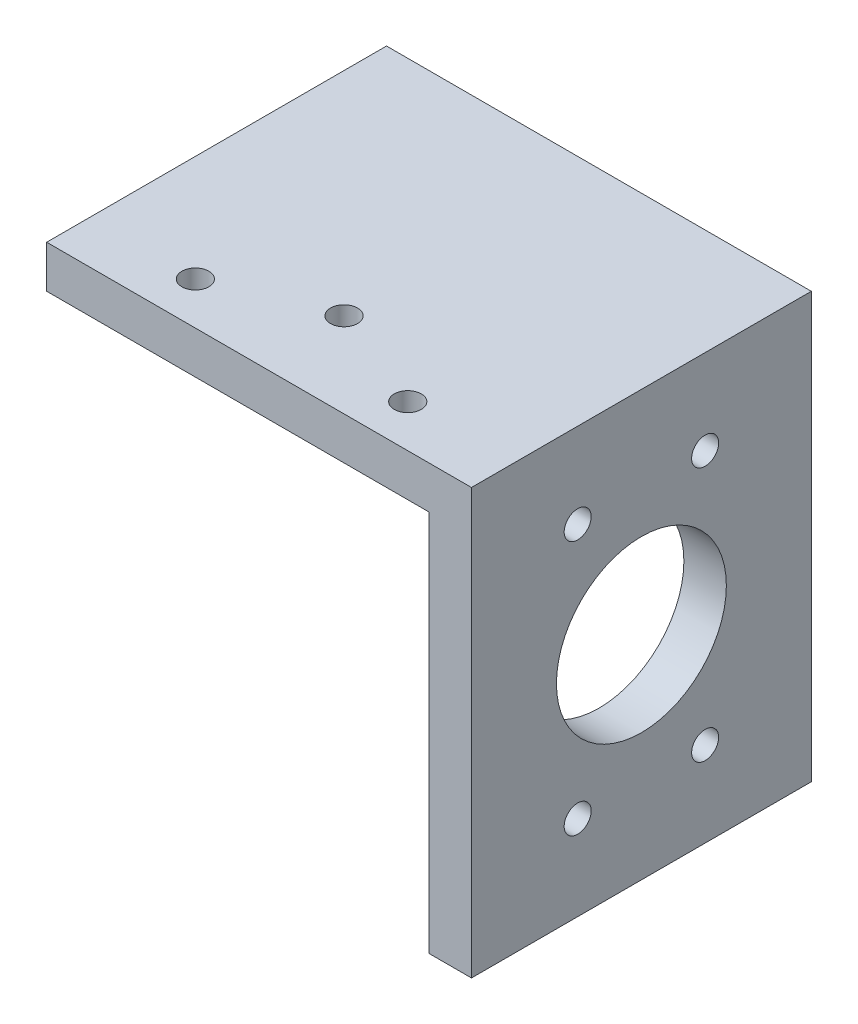
SolidWorks part; units mm, degrees
ref_plane "Front Plane" through (0, 0, 0) normal (0, 0, 1) x (1, 0, 0)
ref_plane "Top Plane" through (0, 0, 0) normal (0, 1, 0) x (1, 0, 0)
ref_plane "Right Plane" through (0, 0, 0) normal (1, 0, 0) x (0, 0, -1)
sketch "Sketch1" plane through (0, 0, 0) normal (0, 0, 1) x (1, 0, 0)
  line L0 (0, 0) -> (63.5, 0)
  line L1 (63.5, 0) -> (63.5, -63.5)
  line L2 (63.5, -63.5) -> (57.15, -63.5)
  line L3 (57.15, -63.5) -> (57.15, -6.35)
  line L4 (57.15, -6.35) -> (0, -6.35)
  line L5 (0, -6.35) -> (0, 0)
  dimension "D1" = 6.35
  dimension "D2" = 6.35
  dimension "D3" = 63.5
  dimension "D4" = 63.5
extrude "Boss-Extrude1" add sketch "Sketch1" along normal blind 50.8
sketch "Sketch2" plane through (63.5, 0, 0) normal (1, 0, 0) x (0, 0, -1)
  line L0 (-50.8, 0) -> (0, 0) construction
  line L5 (-50.8, -63.5) -> (-50.8, 0) construction
  circle A0 centre (-25.4, -31.75) radius 12.7
  dimension "D1" = 25.4
  dimension "D4" = 31.75
  dimension "D5" = 25.4
extrude "Cut-Extrude1" cut sketch "Sketch2" against normal up to next
sketch "Sketch3" plane through (63.5, 0, 0) normal (1, 0, 0) x (0, 0, -1)
  line L0 (-38.1, -31.75) -> (-12.7, -31.75) construction
  line L1 (-34.925, -50.8) -> (-15.875, -50.8) construction
  line L2 (-34.925, -50.8) -> (-34.925, -12.7) construction
  line L3 (-34.925, -12.7) -> (-15.875, -12.7) construction
  line L4 (-15.875, -50.8) -> (-15.875, -12.7) construction
  line L5 (-25.4, -44.45) -> (-25.4, -19.05) construction
  circle A0 centre (-25.4, -31.75) radius 12.7 construction
  point P11 (-25.4, -50.8)
  point P12 (-34.925, -31.75)
  dimension "D1" = 19.05
  dimension "D2" = 38.1
hole_wizard "#10-32 Tapped Hole1" positions "Sketch5" profile "Sketch4" tap size "#10-32" standard "ANSI Inch" end condition up to next
sketch "Sketch5" plane through (63.5, 0, 0) normal (1, 0, 0) x (0, 0, -1)
  point P0 (-34.925, -50.8)
  point P3 (-15.875, -50.8)
  point P6 (-34.925, -12.7)
  point P9 (-15.875, -12.7)
sketch "Sketch4" plane through (63.5, -50.8, 34.925) normal (0, 1, 0) x (0, 0, -1)
  line L0 (0, 0) -> (0, 6.35)
  line L1 (0, 6.35) -> (2.0193, 6.35)
  line L2 (2.0193, 6.35) -> (2.0193, 0)
  line L5 (2.0193, 0) -> (0, 0)
  line L11 (0, -6.35) -> (0, 107.95) construction
  dimension "Thru Tap Drill Dia." = 4.0386
  dimension "Thru Tap Drill Depth" = 6.35
cosmetic thread "Hole Thread1" parameters "D2"=4.826
cosmetic thread "Hole Thread2" parameters "D2"=4.826
cosmetic thread "Hole Thread3" parameters "D2"=4.826
cosmetic thread "Hole Thread4" parameters "D2"=4.826
sketch "Sketch6" plane through (0, 0, 0) normal (0, 1, 0) x (1, 0, 0)
  line L0 (47.625, -44.45) -> (15.875, -44.45) construction
  line L1 (15.875, -44.45) -> (31.75, -38.1) construction
  line L2 (31.75, -38.1) -> (47.625, -44.45) construction
  line L3 (63.5, -50.8) -> (0, -50.8) construction
  point P5 (31.75, -50.8)
  dimension "D1" = 6.35
  dimension "D2" = 6.35
  dimension "D3" = 31.75
hole_wizard "#10-32 Tapped Hole2" positions "Sketch8" profile "Sketch7" tap size "#10-32" standard "ANSI Inch" end condition up to next
sketch "Sketch8" plane through (0, 0, 0) normal (0, 1, 0) x (1, 0, 0)
  point P0 (47.625, -44.45)
  point P3 (31.75, -38.1)
  point P6 (15.875, -44.45)
sketch "Sketch7" plane through (47.625, 0, 44.45) normal (1, 0, 0) x (0, 0, 1)
  line L0 (0, 0) -> (0, 6.35)
  line L1 (0, 6.35) -> (2.0193, 6.35)
  line L2 (2.0193, 6.35) -> (2.0193, 0)
  line L5 (2.0193, 0) -> (0, 0)
  line L11 (0, -6.35) -> (0, 107.95) construction
  dimension "Thru Tap Drill Dia." = 4.0386
  dimension "Thru Tap Drill Depth" = 6.35
cosmetic thread "Hole Thread5" parameters "D2"=4.826
cosmetic thread "Hole Thread6" parameters "D2"=4.826
cosmetic thread "Hole Thread7" parameters "D2"=4.826
sketch "Sketch9" plane through (0, 0, 50.8) normal (0, 0, 1) x (1, 0, 0)
  line L0 (63.5, -59.9116) -> (7.1426, 0)
  line L1 (63.5, -63.5) -> (63.5, 0) construction
  line L2 (63.5, 0) -> (0, 0) construction
  line L3 (7.1426, 0) -> (0, 0)
  line L4 (0, 0) -> (0, -6.35)
  line L5 (0, -6.35) -> (57.15, -63.5)
  line L6 (57.15, -63.5) -> (63.5, -63.5)
  line L7 (63.5, -63.5) -> (63.5, -59.9116)
  line L8 (63.5, -59.9116) -> (64.1122, -59.8813)
